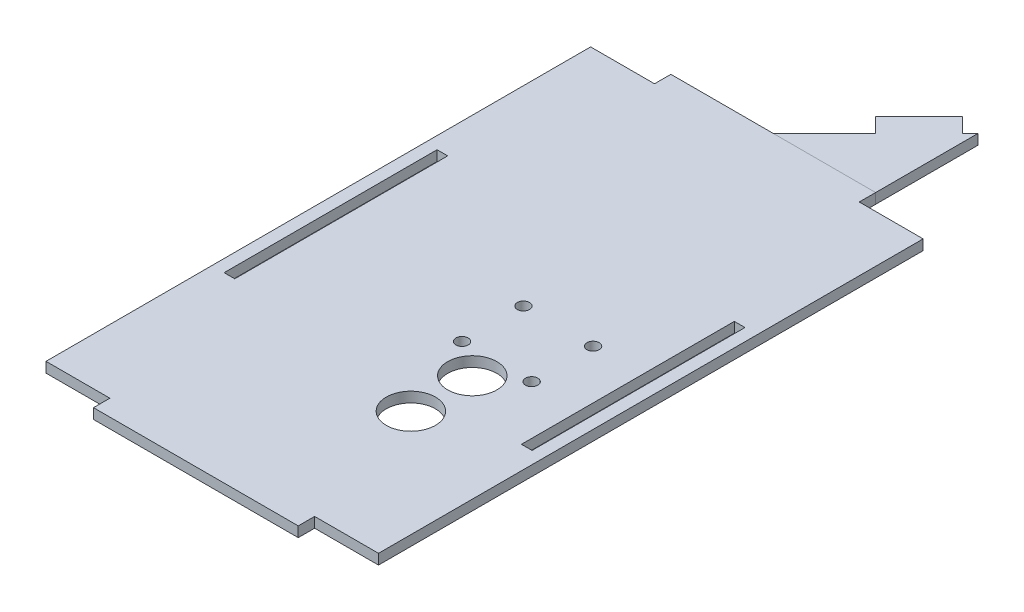
SolidWorks part; units mm, degrees
ref_plane "Front Plane" through (0, 0, 0) normal (0, 0, 1) x (1, 0, 0)
ref_plane "Top Plane" through (0, 0, 0) normal (0, 1, 0) x (1, 0, 0)
ref_plane "Right Plane" through (0, 0, 0) normal (1, 0, 0) x (0, 0, -1)
sketch "Sketch1" plane through (0, 0, 0) normal (0, 1, 0) x (1, 0, 0)
  line L22 (-25, 66.5) -> (-40.6, 66.5)
  line L23 (-40.6, 66.5) -> (-40.6, -66.5)
  line L24 (-40.6, -66.5) -> (-25, -66.5)
  line L25 (-25, -66.5) -> (-25, -70.5)
  line L26 (-25, -70.5) -> (25, -70.5)
  line L27 (-37.6, 26) -> (-35, 26)
  line L28 (-35, -26) -> (-35, 26)
  line L29 (-37.6, -26) -> (-35, -26)
  line L30 (-37.6, -26) -> (-37.6, 26)
  line L31 (0, -112.7216) -> (0, 112.7216) construction
  line L32 (85.5857, 0) -> (-85.5857, 0) construction
  line L33 (25, 66.5) -> (40.6, 66.5)
  line L34 (37.6, -26) -> (37.6, 26)
  line L35 (37.6, -26) -> (35, -26)
  line L36 (35, -26) -> (35, 26)
  line L37 (37.6, 26) -> (35, 26)
  line L38 (40.6, 66.5) -> (40.6, -66.5)
  line L39 (40.6, -66.5) -> (25, -66.5)
  line L40 (25, -66.5) -> (25, -70.5)
  line L41 (25, 66.5) -> (25, 70.5)
  line L42 (-25, 66.5) -> (-25, 70.5)
  line L43 (-25, 70.5) -> (25, 70.5)
  point P27 (-40.6, 0)
  point P46 (0, 0)
  point P49 (0, 0)
  dimension "D2" = 133
  dimension "D3" = 70
  dimension "D4" = 52
  dimension "D5" = 26
  dimension "D7" = 4
  dimension "D8" = 25
  dimension "D9" = 2.6
  dimension "D11" = 2.6
  dimension "D13" = 3
extrude "Boss-Extrude1" add sketch "Sketch1" along normal blind 2.5
sketch "Sketch2" plane through (0, 0, 0) normal (0, -1, 0) x (1, 0, 0)
  line L0 (35, -26) -> (35, 26) construction
  line L12 (25, -70.5) -> (25, -66.5)
  line L13 (25, -66.5) -> (40.6, -66.5)
  line L14 (40.6, -66.5) -> (40.6, 66.5)
  line L15 (40.6, 66.5) -> (25, 66.5)
  line L16 (25, 66.5) -> (25, 70.5)
  line L17 (25, 70.5) -> (-25, 70.5)
  line L18 (-25, 70.5) -> (-25, 66.5)
  line L19 (-25, 66.5) -> (-40.6, 66.5)
  line L20 (-40.6, 66.5) -> (-40.6, -66.5)
  line L21 (-40.6, -66.5) -> (-25, -66.5)
  line L22 (-25, -66.5) -> (-25, -70.5)
  line L23 (-25, -70.5) -> (25, -70.5)
  line L24 (25, -70.5) -> (25, -66.5)
  line L25 (25, -66.5) -> (40.6, -66.5)
  line L26 (40.6, -66.5) -> (40.6, 66.5)
  line L27 (40.6, 66.5) -> (25, 66.5)
  line L28 (25, 66.5) -> (25, 70.5)
  line L29 (25, 70.5) -> (-25, 70.5)
  line L30 (-25, 70.5) -> (-25, 66.5)
  line L31 (-25, 66.5) -> (-40.6, 66.5)
  line L32 (-40.6, 66.5) -> (-40.6, -66.5)
  line L33 (-40.6, -66.5) -> (-25, -66.5)
  line L34 (-25, -66.5) -> (-25, -70.5)
  line L35 (-25, -70.5) -> (25, -70.5)
  circle A0 centre (14.5, 32.5) radius 6
  dimension "D2" = 12
  dimension "D3" = 20.5
  dimension "D4" = 34
  dimension "D1" = 0
extrude "Cut-Extrude1" cut sketch "Sketch2" against normal through all contours A0
sketch "Sketch3" plane through (0, 0, 0) normal (0, -1, 0) x (1, 0, 0)
  line L12 (25, -70.5) -> (25, -66.5)
  line L13 (25, -66.5) -> (40.6, -66.5)
  line L14 (40.6, -66.5) -> (40.6, 66.5)
  line L15 (40.6, 66.5) -> (25, 66.5)
  line L16 (25, 66.5) -> (25, 70.5)
  line L17 (25, 70.5) -> (-25, 70.5)
  line L18 (-25, 70.5) -> (-25, 66.5)
  line L19 (-25, 66.5) -> (-40.6, 66.5)
  line L20 (-40.6, 66.5) -> (-40.6, -66.5)
  line L21 (-40.6, -66.5) -> (-25, -66.5)
  line L22 (-25, -66.5) -> (-25, -70.5)
  line L23 (-25, -70.5) -> (25, -70.5)
  line L24 (25, -70.5) -> (25, -66.5)
  line L25 (25, -66.5) -> (40.6, -66.5)
  line L26 (40.6, -66.5) -> (40.6, 66.5)
  line L27 (40.6, 66.5) -> (25, 66.5)
  line L28 (25, 66.5) -> (25, 70.5)
  line L29 (25, 70.5) -> (-25, 70.5)
  line L30 (-25, 70.5) -> (-25, 66.5)
  line L31 (-25, 66.5) -> (-40.6, 66.5)
  line L32 (-40.6, 66.5) -> (-40.6, -66.5)
  line L33 (-40.6, -66.5) -> (-25, -66.5)
  line L34 (-25, -66.5) -> (-25, -70.5)
  line L35 (-25, -70.5) -> (25, -70.5)
  circle A0 centre (6, 11.5) radius 1.5
  circle A1 centre (23, 11.5) radius 1.5
  circle A2 centre (14.5, 32.5) radius 6 construction
  circle A3 centre (14.5, 32.5) radius 6 construction
  circle A4 centre (14.5, 32.5) radius 6
  dimension "D2" = 21
  dimension "D3" = 21
  dimension "D4" = 3
  dimension "D5" = 3
  dimension "D7" = 8.5
  dimension "D6" = 8.5
  dimension "D1" = 0
extrude "Cut-Extrude2" cut sketch "Sketch3" against normal through all contours A0 | A1
sketch "Sketch4" plane through (0, 2.5, 0) normal (0, 1, 0) x (1, 0, 0)
  line L12 (25, 66.5) -> (25, 70.5)
  line L13 (25, 70.5) -> (-25, 70.5)
  line L14 (-25, 70.5) -> (-25, 66.5)
  line L15 (-25, 66.5) -> (-40.6, 66.5)
  line L16 (-40.6, 66.5) -> (-40.6, -66.5)
  line L17 (-40.6, -66.5) -> (-25, -66.5)
  line L18 (-25, -66.5) -> (-25, -70.5)
  line L19 (-25, -70.5) -> (25, -70.5)
  line L20 (25, -70.5) -> (25, -66.5)
  line L21 (25, -66.5) -> (40.6, -66.5)
  line L22 (40.6, -66.5) -> (40.6, 66.5)
  line L23 (40.6, 66.5) -> (25, 66.5)
  line L24 (25, 66.5) -> (25, 70.5)
  line L25 (25, 70.5) -> (-25, 70.5)
  line L26 (-25, 70.5) -> (-25, 66.5)
  line L27 (-25, 66.5) -> (-40.6, 66.5)
  line L28 (-40.6, 66.5) -> (-40.6, -66.5)
  line L29 (-40.6, -66.5) -> (-25, -66.5)
  line L30 (-25, -66.5) -> (-25, -70.5)
  line L31 (-25, -70.5) -> (25, -70.5)
  line L32 (25, -70.5) -> (25, -66.5)
  line L33 (25, -66.5) -> (40.6, -66.5)
  line L34 (40.6, -66.5) -> (40.6, 66.5)
  line L35 (40.6, 66.5) -> (25, 66.5)
  circle A0 centre (23, -11.5) radius 1.5 construction
  circle A1 centre (6, -11.5) radius 1.5 construction
  circle A2 centre (14.5, -32.5) radius 6 construction
  circle A3 centre (23, -11.5) radius 1.5
  circle A4 centre (6, -11.5) radius 1.5
  circle A5 centre (14.5, -32.5) radius 6
  circle A6 centre (23, 3.5) radius 1.5
  circle A7 centre (14.5, -17.5) radius 6
  circle A8 centre (6, 3.5) radius 1.5
  dimension "D1" = 0
extrude "Cut-Extrude3" cut sketch "Sketch4" against normal through all contours A7 | A8 | A6
sketch "Sketch5" plane through (0, 2.5, 0) normal (0, 1, 0) x (1, 0, 0)
  line L0 (0, 70.5) -> (12.5, 83)
  line L1 (25, 95.5) -> (25, 70.5)
  line L2 (12.5, 83) -> (8.9645, 86.5355)
  line L3 (8.9645, 86.5355) -> (19.5711, 97.1421)
  line L4 (19.5711, 97.1421) -> (23.1066, 93.6066)
  line L5 (23.1066, 93.6066) -> (25, 95.5)
  line L12 (25, 66.5) -> (25, 70.5)
  line L13 (25, 70.5) -> (-25, 70.5)
  line L14 (-25, 70.5) -> (-25, 66.5)
  line L15 (-25, 66.5) -> (-40.6, 66.5)
  line L16 (-40.6, 66.5) -> (-40.6, -66.5)
  line L17 (-40.6, -66.5) -> (-25, -66.5)
  line L18 (-25, -66.5) -> (-25, -70.5)
  line L19 (-25, -70.5) -> (25, -70.5)
  line L20 (25, -70.5) -> (25, -66.5)
  line L21 (25, -66.5) -> (40.6, -66.5)
  line L22 (40.6, -66.5) -> (40.6, 66.5)
  line L23 (40.6, 66.5) -> (25, 66.5)
  line L24 (25, 66.5) -> (25, 70.5)
  line L25 (25, 70.5) -> (-25, 70.5)
  line L26 (-25, 70.5) -> (-25, 66.5)
  line L27 (-25, 66.5) -> (-40.6, 66.5)
  line L28 (-40.6, 66.5) -> (-40.6, -66.5)
  line L29 (-40.6, -66.5) -> (-25, -66.5)
  line L30 (-25, -66.5) -> (-25, -70.5)
  line L31 (-25, -70.5) -> (25, -70.5)
  line L32 (25, -70.5) -> (25, -66.5)
  line L33 (25, -66.5) -> (40.6, -66.5)
  line L34 (40.6, -66.5) -> (40.6, 66.5)
  line L35 (40.6, 66.5) -> (25, 66.5)
  line M26 (25, 70.5) -> (-25, 70.5)
  dimension "D2" = 45
  dimension "D3" = 15
  dimension "D4" = 5
  dimension "D1" = 0
extrude "Boss-Extrude2" add sketch "Sketch5" against normal blind 2.5 separate body contours L1 L0 M26
